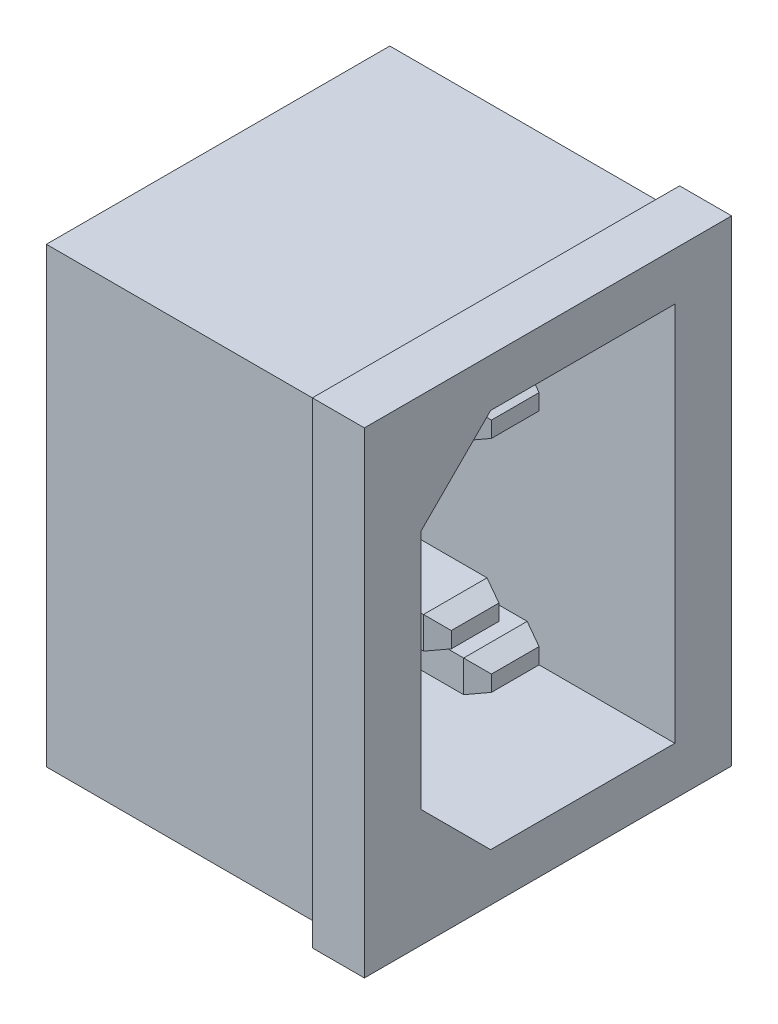
SolidWorks part; units mm, degrees
ref_plane "Front Plane" through (0, 0, 0) normal (0, 0, 1) x (1, 0, 0)
ref_plane "Top Plane" through (0, 0, 0) normal (0, 1, 0) x (1, 0, 0)
ref_plane "Right Plane" through (0, 0, 0) normal (1, 0, 0) x (0, 0, -1)
sketch "Sketch1" plane through (0, 0, 0) normal (1, 0, 0) x (0, 0, -1)
  line L1 (11.7475, 15.24) -> (-11.7475, 15.24)
  line L2 (11.7475, 15.24) -> (11.7475, -15.24)
  line L3 (11.7475, -15.24) -> (-11.7475, -15.24)
  line L4 (-11.7475, 15.24) -> (-11.7475, -15.24)
  line L5 (11.7475, 15.24) -> (-11.7475, -15.24) construction
  line L6 (11.7475, -15.24) -> (-11.7475, 15.24) construction
  point P0 (0, 0)
  dimension "D1" = 23.495
  dimension "D2" = 30.48
extrude "Boss-Extrude1" add sketch "Sketch1" along normal blind 3.3274
sketch "Sketch2" plane through (0, 0, 0) normal (-1, 0, 0) x (0, 0, 1)
  line L0 (-11.7475, 15.24) -> (11.7475, 15.24) construction
  line L1 (-10.9855, -14.478) -> (10.9855, -14.478)
  line L2 (-10.9855, -14.478) -> (-10.9855, 14.478)
  line L3 (-10.9855, 14.478) -> (10.9855, 14.478)
  line L4 (10.9855, -14.478) -> (10.9855, 14.478)
  line L5 (-10.9855, -14.478) -> (10.9855, 14.478) construction
  line L6 (-10.9855, 14.478) -> (10.9855, -14.478) construction
  line L7 (-11.7475, -15.24) -> (-11.7475, 15.24) construction
  point P0 (0, 0)
  dimension "D1" = 0.762
  dimension "D2" = 0.762
extrude "Boss-Extrude2" add sketch "Sketch2" along normal blind 17.78
sketch "Sketch3" plane through (3.3274, 0, 0) normal (1, 0, 0) x (0, 0, -1)
  line L0 (-11.7475, 15.24) -> (-11.7475, -15.24) construction
  line L1 (8.1153, 12.1666) -> (-8.1153, 12.1666)
  line L2 (8.1153, 12.1666) -> (8.1153, -12.1666)
  line L3 (8.1153, -12.1666) -> (-8.1153, -12.1666)
  line L4 (-8.1153, 12.1666) -> (-8.1153, -12.1666)
  line L5 (8.1153, 12.1666) -> (-8.1153, -12.1666) construction
  line L6 (8.1153, -12.1666) -> (-8.1153, 12.1666) construction
  line L7 (11.7475, 15.24) -> (-11.7475, 15.24) construction
  point P0 (0, 0)
  dimension "D1" = 3.6322
  dimension "D2" = 3.0734
extrude "Cut-Extrude1" cut sketch "Sketch3" against normal blind 16.51
chamfer "Chamfer1" distance 4.445 angle 45 2 edges at (-4.9276, 12.1666, 8.1153) (-4.9276, -12.1666, 8.1153)
ref_plane "Plane1" through (2.8194, 0, 0) normal (1, 0, 0) x (0, 0, -1)
sketch "Sketch4" plane through (2.8194, 0, 0) normal (1, 0, 0) x (0, 0, -1)
  line L1 (-6.1875, -0.8002) -> (-2.1235, -0.8002)
  line L2 (-6.1875, -0.8002) -> (-6.1875, 1.2318)
  line L3 (-6.1875, 1.2318) -> (-2.1235, 1.2318)
  line L4 (-2.1235, -0.8002) -> (-2.1235, 1.2318)
  line L5 (-6.1875, -0.8002) -> (-2.1235, 1.2318) construction
  line L6 (-6.1875, 1.2318) -> (-2.1235, -0.8002) construction
  point P0 (-4.1555, 0.2158)
  dimension "D1" = 2.032
  dimension "D2" = 4.064
extrude "Boss-Extrude3" add sketch "Sketch4" against normal up to surface (16.002 mm away) up to face at (-13.1826, 0, 1.2234)
chamfer "Chamfer2" distance 1.27 distance2 0.508 2 edges at (2.8194, -0.8002, 4.1555) (2.8194, 1.2318, 4.1555)
chamfer "Chamfer3" distance 1.27 distance2 0.508 2 edges at (2.8194, 0.2158, 2.1235) (2.8194, 0.2158, 6.1875)
ref_plane "Plane2" through (-0.7366, 0, 0) normal (1, 0, 0) x (0, 0, -1)
sketch "Sketch5" plane through (-0.7366, 0, 0) normal (1, 0, 0) x (0, 0, -1)
  line L0 (8.1153, 12.1666) -> (-3.6703, 12.1666) construction
  line L1 (-0.0635, 6.0198) -> (4.0005, 6.0198)
  line L2 (-0.0635, 6.0198) -> (-0.0635, 8.0518)
  line L3 (-0.0635, 8.0518) -> (4.0005, 8.0518)
  line L4 (4.0005, 6.0198) -> (4.0005, 8.0518)
  line L5 (-0.0635, 6.0198) -> (4.0005, 8.0518) construction
  line L6 (-0.0635, 8.0518) -> (4.0005, 6.0198) construction
  line L7 (8.1153, -12.1666) -> (8.1153, 12.1666) construction
  point P0 (1.9685, 7.0358)
  dimension "D1" = 4.064
  dimension "D2" = 2.032
  dimension "D3" = 4.1148
  dimension "D4" = 4.1148
extrude "Boss-Extrude4" add sketch "Sketch5" against normal up to surface (12.446 mm away) up to face at (-13.1826, 0.2158, 4.1555)
chamfer "Chamfer4" distance 1.27 distance2 0.508 4 edges at (-0.7366, 7.0358, -4.0005) (-0.7366, 6.0198, -1.9685) (-0.7366, 7.0358, 0.0635) (-0.7366, 8.0518, -1.9685)
ref_plane "Plane3" through (0, 0, 0) normal (0, 1, 0) x (1, 0, 0)
mirror "Mirror7" about plane through (0, 0, 0) normal (0, 1, 0) of "Boss-Extrude4"
chamfer "Chamfer5" distance 0.508 distance2 1.27 4 edges at (-0.7366, -7.0358, -4.0005) (-0.7366, -6.0198, -1.9685) (-0.7366, -7.0358, 0.0635) (-0.7366, -8.0518, -1.9685)
